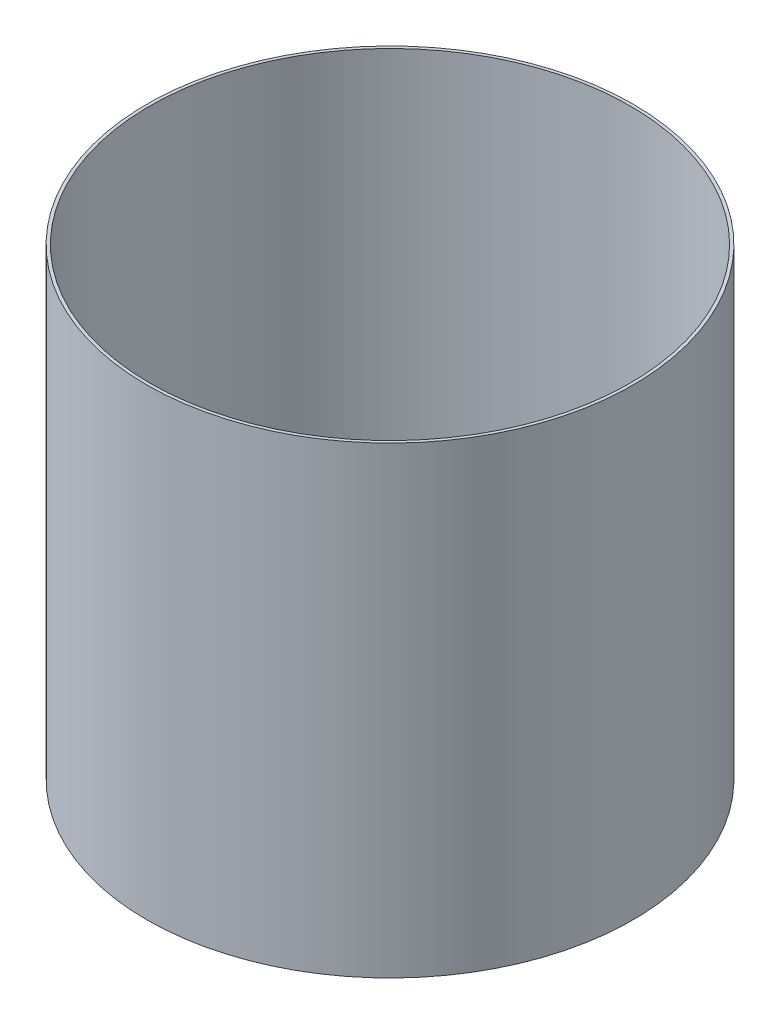
SolidWorks part; units mm, degrees
material "Air"
ref_plane "Front Plane" through (0, 0, 0) normal (0, 0, 1) x (1, 0, 0)
ref_plane "Top Plane" through (0, 0, 0) normal (0, 1, 0) x (1, 0, 0)
ref_plane "Right Plane" through (0, 0, 0) normal (1, 0, 0) x (0, 0, -1)
sketch "Sketch1" plane through (0, 0, 0) normal (0, 1, 0) x (1, 0, 0)
  circle A0 centre (0, 0) radius 39.5
  circle A1 centre (0, 0) radius 40
  dimension "D1" = 80
  dimension "D2" = 79
extrude "Boss-Extrude1" add sketch "Sketch1" along normal blind 76.2
